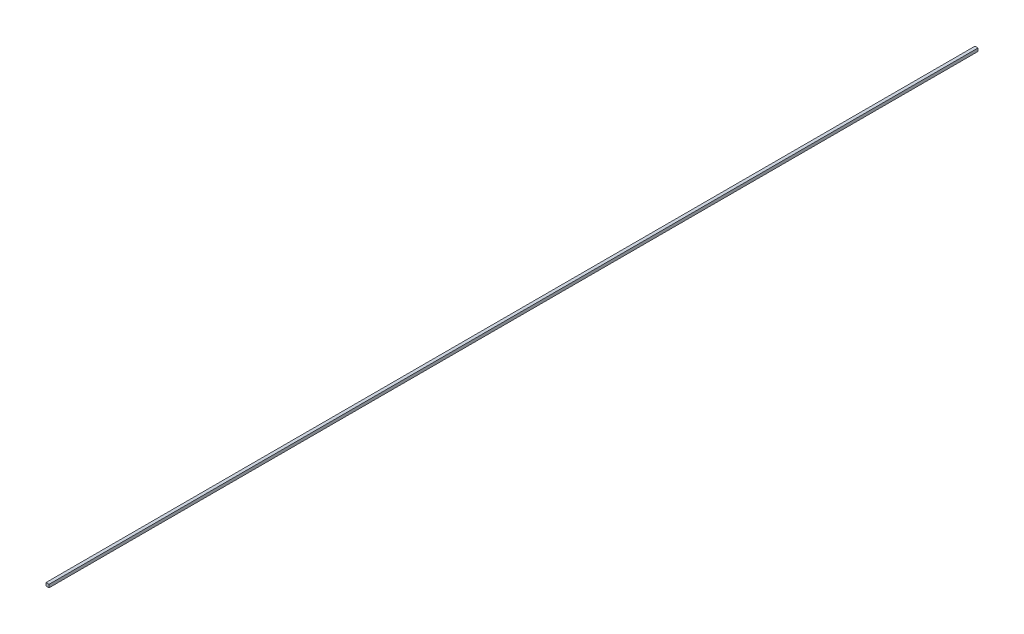
SolidWorks part; units mm, degrees
material "ﾊﾞﾙｻ"
ref_plane "正面" through (0, 0, 0) normal (0, 0, 1) x (1, 0, 0)
ref_plane "平面" through (0, 0, 0) normal (0, 1, 0) x (1, 0, 0)
ref_plane "右側面" through (0, 0, 0) normal (1, 0, 0) x (0, 0, -1)
sketch "ｽｹｯﾁ1" plane through (0, 0, 0) normal (0, 0, 1) x (1, 0, 0)
  line L1 (-1, 1) -> (1, 1)
  line L2 (-1, 1) -> (-1, -1)
  line L3 (-1, -1) -> (1, -1)
  line L4 (1, 1) -> (1, -1)
  line L5 (-1, 1) -> (1, -1) construction
  line L6 (-1, -1) -> (1, 1) construction
  point P0 (0, 0)
  dimension "D1" = 2
extrude "ﾎﾞｽ - 押し出し1" add sketch "ｽｹｯﾁ1" along normal blind 604.67
